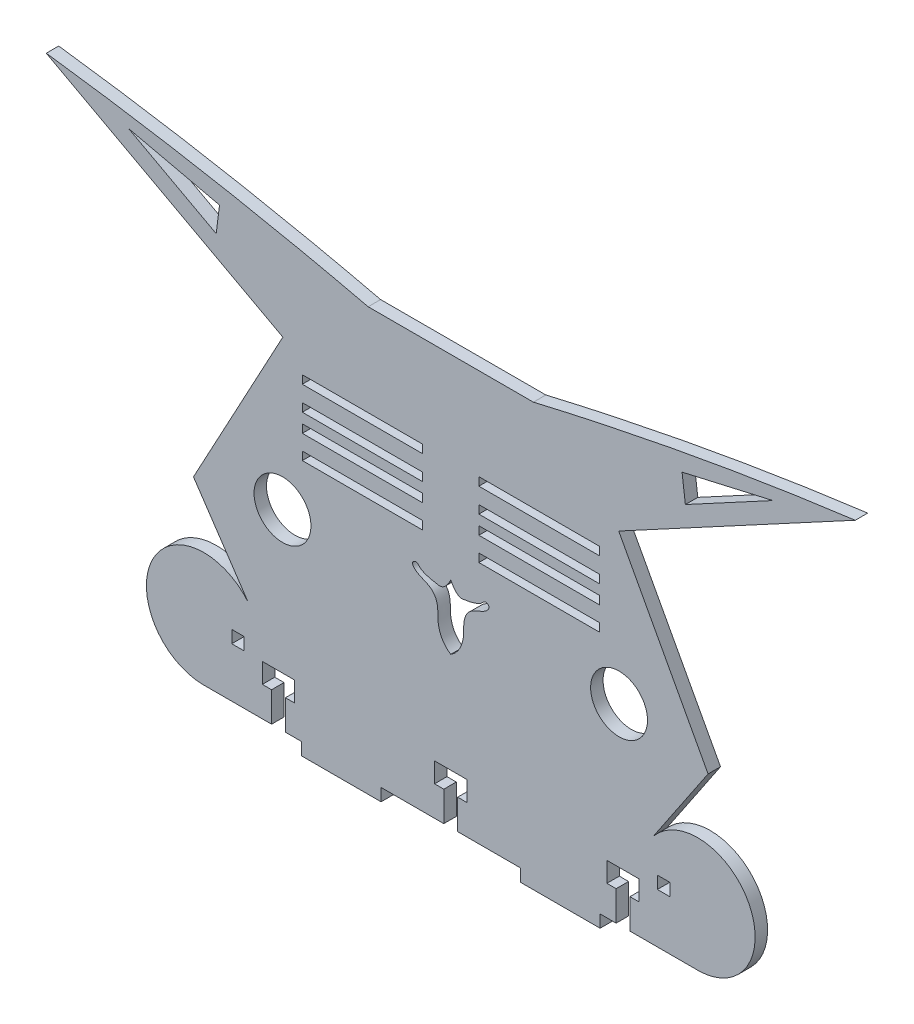
SolidWorks part; units mm, degrees
ref_plane "Front Plane" through (0, 0, 0) normal (0, 0, 1) x (1, 0, 0)
ref_plane "Top Plane" through (0, 0, 0) normal (0, 1, 0) x (1, 0, 0)
ref_plane "Right Plane" through (0, 0, 0) normal (1, 0, 0) x (0, 0, -1)
sketch "Sketch1" plane through (0, 0, 0) normal (0, 0, 1) x (1, 0, 0)
  line L0 (-1.0054, -59.1781) -> (62.4946, -59.1781)
  line L1 (50.6891, -35.2122) -> (64.6406, -14.4814)
  line L2 (64.6406, -14.4814) -> (41.8391, 27.7878)
  line L3 (41.8391, 27.7878) -> (102.1972, 60.3471)
  line L4 (20.0705, 45.3844) -> (-1.0054, 45.3844)
  line L5 (-1.0054, 45.3844) -> (-1.0054, -59.1781)
  arc A0 (62.4946, -59.1781) -> (50.6891, -35.2122) centre (61.9964, -44.5329) ccw
  spline S0 degree 2 poles (102.1972, 60.3471) (60.7427, 54.9669) (20.0705, 45.3844) knots 0 0 0 1 1 1
  point P1 (50.0935, -35.4507)
  point P9 (0, 0)
  point P12 (63.2452, -62.7691)
  point P13 (0, 0)
  point P14 (47.4441, -42.1433)
  point P15 (54.7887, -30.9019)
  point P16 (50.704, -36.8515)
  point P17 (50.6891, -35.2122)
  dimension "D6" = 68.58
  dimension "D1" = 63.5
extrude "Boss-Extrude1" add sketch "Sketch1" along normal blind 3.175 contours L3 S0 L4 L5 L0 A0 L1 L2
sketch "Sketch6" plane through (0, 0, 0) normal (0, 0, 1) x (1, 0, 0)
  line L0 (57.9966, 48.8872) -> (81.1804, 54.1944)
  line L1 (81.1804, 54.1944) -> (58.8471, 42.1469)
  line L2 (58.8471, 42.1469) -> (57.9966, 48.8872)
  line L5 (-1.0054, -4.4608) -> (-1.0054, -20.8685)
  circle A0 centre (41.9283, -10.3631) radius 7.2572
  spline S1 degree 3 poles (-1.0054, -4.4608) (0.9101, -8.0876) (2.1636, -6.9443) (3.7592, -6.9043) (6.9825, -5.9657) (7.1079, -4.954) (8.3837, -4.7793) (8.8584, -5.5979) (8.0599, -7.2665) (5.3875, -7.7433) (2.876, -9.7384) (2.1658, -12.4377) (2.5023, -16.4602) (0.9297, -19.7009) (-1.0054, -20.8685) knots 0 0 0 0 0.201891 0.229 0.271089 0.343452 0.384031 0.405551 0.412268 0.551583 0.622209 0.702728 0.796796 1 1 1 1
  point P15 (20.5591, 16.2408)
  point P17 (0, 0)
  point P19 (0, 0)
  point P21 (0, 0)
  point P23 (0, 0)
  point P25 (16.5435, 16.2408)
  point P27 (20.3478, 13.8103)
  point P29 (18.5513, 10.7458)
  point P31 (16.0313, 11.3032)
  point P33 (0, 0)
  point P35 (19.2676, 15.5851)
  point P37 (22.7986, 16.6168)
  point P38 (25.4436, 19.4822)
  point P41 (30.5959, 20.0433)
  point P42 (26.3253, 15.7351)
  point P43 (29.6316, 19.1516)
  point P44 (26.9866, 15.9555)
  point P45 (18.2641, 15.1092)
  point P46 (13.7608, 16.0462)
  point P47 (17.9287, 12.714)
  point P48 (39.9961, -15.726)
  point P49 (4.5037, -18.2871)
  point P50 (2.9755, -14.3869)
  point P51 (3.4588, -17.7702)
  point P52 (4.1838, -16.864)
  point P53 (2.7942, -16.6223)
  point P54 (1.888, -12.816)
  point P55 (2.613, -13.4202)
  point P56 (1.5255, -22.4828)
  point P57 (47.731, -10.2662)
  point P58 (16.5772, 20.0194)
  point P59 (14.5251, 17.5892)
  point P60 (13.661, 15.3751)
  point P61 (10.6947, -7.2211)
  point P62 (10.6248, -6.8017)
  point P63 (8.2928, -7.9889)
  point P64 (6.2798, -9.4035)
  point P65 (10.0484, -6.1576)
  point P66 (6.2401, -8.54)
  point P67 (9.7328, -6.1103)
  point P68 (8.4268, -5.2295)
  point P69 (8.3965, -5.5636)
  point P70 (7.1816, -6.0496)
  point P71 (8.6698, -6.2014)
  point P72 (3.7408, -9.6208)
  point P73 (2.2462, -12.7344)
  point P74 (2.1217, -15.7649)
  point P75 (3.0519, -10.2662)
  point P76 (5.9533, -6.168)
  point P77 (7.536, -4.9889)
  point P78 (35.8043, -8.326)
  point P79 (41.9283, -10.3631)
extrude "Cut-Extrude5" cut sketch "Sketch6" along normal blind 3.175
sketch "Sketch9" plane through (0, 0, 0) normal (0, 0, -1) x (-1, 0, 0)
  line L1 (-54.8746, -46.4781) -> (-51.6996, -46.4781)
  line L2 (-54.8746, -46.4781) -> (-54.8746, -43.3031)
  line L3 (-54.8746, -43.3031) -> (-51.6996, -43.3031)
  line L4 (-51.6996, -46.4781) -> (-51.6996, -43.3031)
  line L5 (-54.8746, -46.4781) -> (-51.6996, -43.3031) construction
  line L6 (-54.8746, -43.3031) -> (-51.6996, -46.4781) construction
  line L7 (1.0054, -59.1781) -> (-62.4946, -59.1781) construction
  point P0 (-53.2871, -44.8906)
  point P5 (70.9816, -45.599)
  point P9 (57.9523, -48.042)
  dimension "D1" = 12.7
  dimension "D2" = 3.175
  dimension "D3" = 7.62
extrude "Cut-Extrude7" cut sketch "Sketch9" against normal blind 3.175
sketch "Sketch8" plane through (0, 0, 0) normal (0, 0, 1) x (1, 0, 0)
  line L0 (-1.0054, 45.3844) -> (-1.0054, -4.4608) construction
  line L1 (-8.1635, 21.9675) -> (-38.888, 21.9675)
  line L2 (-8.1635, 21.9675) -> (-8.1635, 19.859)
  line L3 (-8.1635, 19.859) -> (-38.888, 19.859)
  line L4 (-38.888, 21.9675) -> (-38.888, 19.859)
  line L5 (-8.1635, 15.7925) -> (-38.888, 15.7925)
  line L6 (-8.1635, 15.7925) -> (-8.1635, 13.6839)
  line L7 (-8.1635, 13.6839) -> (-38.888, 13.6839)
  line L8 (-38.888, 15.7925) -> (-38.888, 13.6839)
  line L9 (-8.1635, 11.1235) -> (-38.888, 11.1235)
  line L10 (-8.1635, 11.1235) -> (-8.1635, 9.015)
  line L11 (-8.1635, 9.015) -> (-38.888, 9.015)
  line L12 (-38.888, 11.1235) -> (-38.888, 9.015)
  line L13 (-8.1635, 5.0991) -> (-38.888, 5.0991)
  line L14 (-8.1635, 5.0991) -> (-8.1635, 2.9906)
  line L15 (-8.1635, 2.9906) -> (-38.888, 2.9906)
  line L16 (-38.888, 5.0991) -> (-38.888, 2.9906)
  line L17 (36.8772, 5.0991) -> (36.8772, 2.9906)
  line L18 (6.1527, 2.9906) -> (36.8772, 2.9906)
  line L19 (6.1527, 5.0991) -> (6.1527, 2.9906)
  line L20 (6.1527, 5.0991) -> (36.8772, 5.0991)
  line L21 (36.8772, 11.1235) -> (36.8772, 9.015)
  line L22 (6.1527, 9.015) -> (36.8772, 9.015)
  line L23 (6.1527, 11.1235) -> (6.1527, 9.015)
  line L24 (6.1527, 11.1235) -> (36.8772, 11.1235)
  line L25 (36.8772, 15.7925) -> (36.8772, 13.6839)
  line L26 (6.1527, 13.6839) -> (36.8772, 13.6839)
  line L27 (6.1527, 15.7925) -> (6.1527, 13.6839)
  line L28 (6.1527, 15.7925) -> (36.8772, 15.7925)
  line L29 (36.8772, 21.9675) -> (36.8772, 19.859)
  line L30 (6.1527, 19.859) -> (36.8772, 19.859)
  line L31 (6.1527, 21.9675) -> (6.1527, 19.859)
  line L32 (6.1527, 21.9675) -> (36.8772, 21.9675)
extrude "Cut-Extrude6" cut sketch "Sketch8" along normal blind 3.175
mirror "Mirror4" about plane through (-1.0054, 0, 3.175) normal (1, 0, 0) of "Cut-Extrude7", "Cut-Extrude6", "Boss-Extrude1", "Cut-Extrude5"
sketch "Sketch10" plane through (0, -59.1781, 0) normal (0, -1, 0) x (1, 0, 0)
  line L0 (-64.5054, 0) -> (62.4946, 0) construction
  line L1 (-39.1054, 3.175) -> (-18.7854, 3.175)
  line L2 (-39.1054, 3.175) -> (-39.1054, 0)
  line L3 (-39.1054, 0) -> (-18.7854, 0)
  line L4 (-18.7854, 3.175) -> (-18.7854, 0)
  line L5 (-39.1054, 3.175) -> (-18.7854, 0) construction
  line L6 (-39.1054, 0) -> (-18.7854, 3.175) construction
  line L7 (-64.5054, 3.175) -> (62.4946, 3.175) construction
  line L8 (-64.5054, 3.175) -> (-64.5054, 0) construction
  line L9 (-1.0054, 20.7144) -> (-1.0054, -22.6503) construction
  line L10 (37.0946, 0) -> (16.7746, 3.175) construction
  line L11 (37.0946, 3.175) -> (16.7746, 0) construction
  line L12 (16.7746, 3.175) -> (16.7746, 0)
  line L13 (37.0946, 0) -> (16.7746, 0)
  line L14 (37.0946, 3.175) -> (37.0946, 0)
  line L15 (37.0946, 3.175) -> (16.7746, 3.175)
  point P0 (-28.9454, 1.5875)
  point P11 (-64.5054, 1.5875)
  point P19 (26.9346, 1.5875)
  dimension "D1" = 20.32
  dimension "D2" = 25.4
  dimension "D3" = 63.5
extrude "Boss-Extrude2" add sketch "Sketch10" along normal blind 3.175
sketch "Sketch11" plane through (0, 0, 3.175) normal (0, 0, 1) x (1, 0, 0)
  line L0 (-49.0876, -51.5581) -> (-49.0876, -46.4781)
  line L1 (-49.0876, -46.4781) -> (-40.8326, -46.4781)
  line L2 (-40.8326, -46.4781) -> (-40.8326, -51.5581)
  line L3 (-40.8326, -51.5581) -> (-43.1948, -51.5581)
  line L4 (-43.1948, -51.5581) -> (-43.1948, -59.1781)
  line L5 (-64.5054, -59.1781) -> (-39.1054, -59.1781) construction
  line L6 (-43.1948, -59.1781) -> (-46.7254, -59.1781)
  line L7 (-46.7254, -59.1781) -> (-46.7254, -51.5581)
  line L8 (-46.7254, -51.5581) -> (-49.0876, -51.5581)
  line L9 (-5.1456, -51.5581) -> (-5.1456, -46.4781)
  line L10 (-5.1456, -46.4781) -> (3.1094, -46.4781)
  line L11 (3.1094, -46.4781) -> (3.1094, -51.5581)
  line L12 (3.1094, -51.5581) -> (0.7472, -51.5581)
  line L13 (0.7472, -51.5581) -> (0.7472, -59.1781)
  line L14 (0.7472, -59.1781) -> (-2.7834, -59.1781)
  line L15 (-2.7834, -59.1781) -> (-2.7834, -51.5581)
  line L16 (-2.7834, -51.5581) -> (-5.1456, -51.5581)
  line L17 (38.8218, -51.5581) -> (38.8218, -46.4781)
  line L18 (38.8218, -46.4781) -> (47.0768, -46.4781)
  line L19 (47.0768, -46.4781) -> (47.0768, -51.5581)
  line L20 (47.0768, -51.5581) -> (44.7146, -51.5581)
  line L21 (44.7146, -51.5581) -> (44.7146, -59.1781)
  line L22 (44.7146, -59.1781) -> (41.184, -59.1781)
  line L23 (41.184, -59.1781) -> (41.184, -51.5581)
  line L24 (41.184, -51.5581) -> (38.8218, -51.5581)
  line L25 (-18.7854, -62.3531) -> (-18.7854, -59.1781) construction
  dimension "D1" = 8.255
  dimension "D2" = 5.08
  dimension "D3" = 3.5306
  dimension "D4" = 7.62
  dimension "D5" = 17.78
  dimension "D8" = 17.78
  dimension "D9" = 16.002
  dimension "D6" = 2
  dimension "D7" = 2
extrude "Cut-Extrude8" cut sketch "Sketch11" against normal blind 3.175
